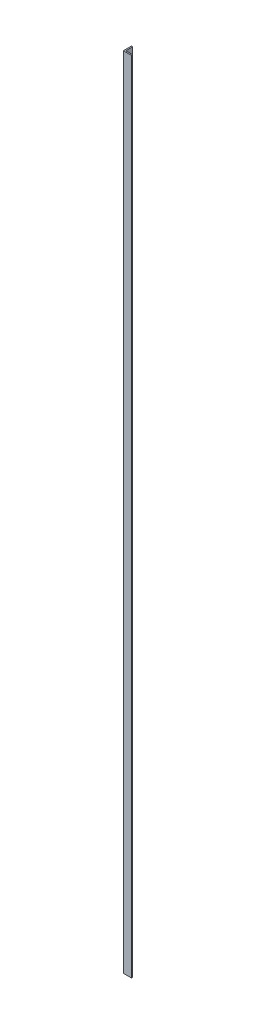
SolidWorks part; units mm, degrees
ref_plane "Front Plane" through (0, 0, 0) normal (0, 0, 1) x (1, 0, 0)
ref_plane "Top Plane" through (0, 0, 0) normal (0, 1, 0) x (1, 0, 0)
ref_plane "Right Plane" through (0, 0, 0) normal (1, 0, 0) x (0, 0, -1)
sketch "Sketch1" plane through (0, 0, 0) normal (0, 1, 0) x (1, 0, 0)
  line L2 (0, 0) -> (0, 50.8)
  line L3 (0, 50.8) -> (7.62, 50.8)
  line L4 (7.62, 7.62) -> (7.62, 50.8)
  line L5 (0, 0) -> (50.8, 0)
  line L7 (7.62, 7.62) -> (50.8, 7.62)
  line L8 (50.8, 0) -> (50.8, 7.62)
  dimension "D1" = 50.8
  dimension "D2" = 7.62
  dimension "D3" = 50.8
  dimension "D4" = 7.62
extrude "Boss-Extrude1" add sketch "Sketch1" along normal blind 4978.4
equation "\"in\"=1.0212"
